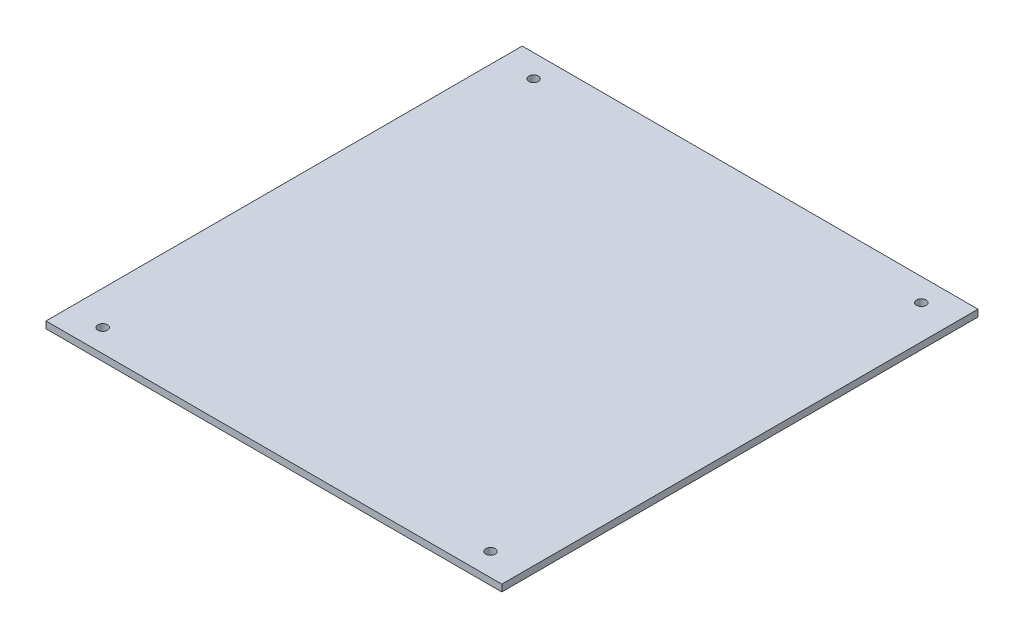
SolidWorks part; units mm, degrees
ref_plane "Alzado" through (0, 0, 0) normal (0, 0, 1) x (1, 0, 0)
ref_plane "Planta" through (0, 0, 0) normal (0, 1, 0) x (1, 0, 0)
ref_plane "Vista lateral" through (0, 0, 0) normal (1, 0, 0) x (0, 0, -1)
sketch "Croquis1" plane through (0, 0, 0) normal (0, 1, 0) x (1, 0, 0)
  line L1 (-100.5, 105) -> (100.5, 105)
  line L2 (-100.5, 105) -> (-100.5, -105)
  line L3 (-100.5, -105) -> (100.5, -105)
  line L4 (100.5, 105) -> (100.5, -105)
  line L5 (-100.5, 105) -> (100.5, -105) construction
  line L6 (-100.5, -105) -> (100.5, 105) construction
  line L7 (-85.5, 95) -> (85.5, 95) construction
  line L8 (-85.5, 95) -> (-85.5, -95) construction
  line L9 (-85.5, -95) -> (85.5, -95) construction
  line L10 (85.5, 95) -> (85.5, -95) construction
  line L11 (-85.5, 95) -> (85.5, -95) construction
  line L12 (-85.5, -95) -> (85.5, 95) construction
  circle A0 centre (-85.5, 95) radius 2.1
  circle A1 centre (85.5, 95) radius 2.1
  circle A2 centre (85.5, -95) radius 2.1
  circle A3 centre (-85.5, -95) radius 2.1
  point P0 (0, 0)
  point P5 (0, 0)
  point P16 (85.5, 97.7913)
  dimension "D5" = 4.2
  dimension "D1" = 190
  dimension "D2" = 171
  dimension "D3" = 10
  dimension "D4" = 15
extrude "Saliente-Extruir1" add sketch "Croquis1" along normal blind 3
